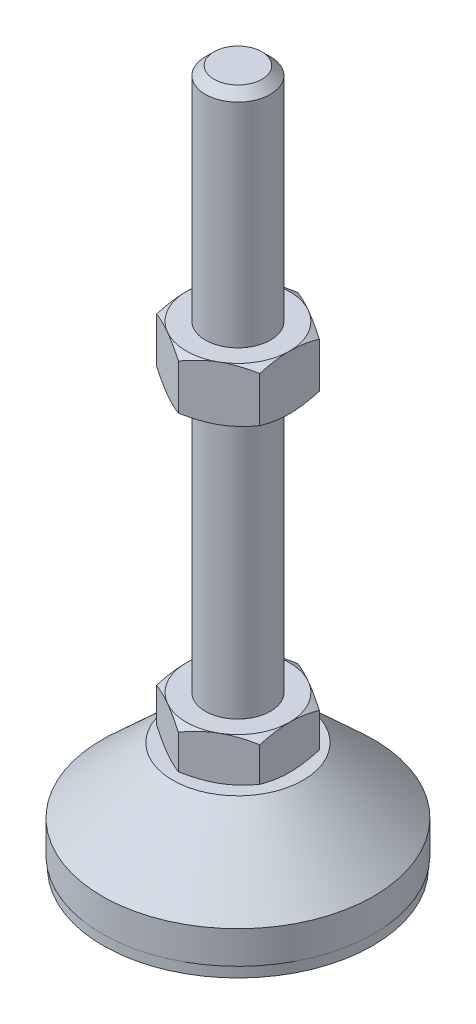
SolidWorks part; units mm, degrees
ref_plane "Спереди" through (0, 0, 0) normal (0, 0, 1) x (1, 0, 0)
ref_plane "Сверху" through (0, 0, 0) normal (0, 1, 0) x (1, 0, 0)
ref_plane "Справа" through (0, 0, 0) normal (1, 0, 0) x (0, 0, -1)
sketch "Эскиз1" plane through (0, 0, 0) normal (0, 0, 1) x (1, 0, 0)
  line L0 (0, 0) -> (-24.8, 0)
  line L1 (-24.8, 0) -> (-24.8, 2)
  line L2 (-24.8, 2) -> (-25, 2)
  line L3 (-25, 2) -> (-25, 8)
  line L4 (-25, 8) -> (-12, 20)
  line L5 (-12, 20) -> (-6, 20)
  line L12 (-6, 28) -> (-6, 126.4)
  line L13 (-6, 126.4) -> (-4.4, 128)
  line L14 (-4.4, 128) -> (0, 128)
  line L15 (0, 128) -> (0, 0) construction
  line L16 (-6, 20) -> (0, 20) construction
  line L17 (0, 0) -> (0, 128)
  line L18 (0, 0) -> (0, -7.9595) construction
  line L19 (-6, 28) -> (-6, 20)
  point P8 (-6, 77.2)
  point P23 (-9, 20)
  dimension "D1" = 12
  dimension "D2" = 20
  dimension "D3" = 8
  dimension "D4" = 50
  dimension "D5" = 6
  dimension "D6" = 1.6
  dimension "D7" = 45
  dimension "D8" = 24
  dimension "D9" = 2
  dimension "D10" = 100
  dimension "D11" = 6
  dimension "D12" = 0.2
revolve "Повернуть1" add sketch "Эскиз1" angle 360 about L17
sketch "Эскиз2" plane through (0, 20, 0) normal (0, 1, 0) x (1, 0, 0)
  line L1 (0, 10.9697) -> (-9.5, 5.4848)
  line L2 (-9.5, 5.4848) -> (-9.5, -5.4848)
  line L3 (-9.5, -5.4848) -> (0, -10.9697)
  line L4 (0, -10.9697) -> (9.5, -5.4848)
  line L5 (9.5, -5.4848) -> (9.5, 5.4848)
  line L6 (9.5, 5.4848) -> (0, 10.9697)
  circle A0 centre (0, 0) radius 9.5 construction
  dimension "D1" = 19
extrude "Бобышка-Вытянуть1" add sketch "Эскиз2" along normal up to vertex (8 mm away) up to point (-6, 28, 0)
ref_plane "Плоскость1" through (0, 77.2, 0) normal (0, 1, 0) x (1, 0, 0)
sketch "Эскиз3" plane through (0, 77.2, 0) normal (0, 1, 0) x (1, 0, 0)
  line L6 (9.5, 5.4848) -> (0, 10.9697)
  line L7 (0, 10.9697) -> (-9.5, 5.4848)
  line L8 (-9.5, 5.4848) -> (-9.5, -5.4848)
  line L9 (-9.5, -5.4848) -> (0, -10.9697)
  line L10 (0, -10.9697) -> (9.5, -5.4848)
  line L11 (9.5, -5.4848) -> (9.5, 5.4848)
  line L12 (9.5, 5.4848) -> (0, 10.9697)
  line L13 (0, 10.9697) -> (-9.5, 5.4848)
  line L14 (-9.5, 5.4848) -> (-9.5, -5.4848)
  line L15 (-9.5, -5.4848) -> (0, -10.9697)
  line L16 (0, -10.9697) -> (9.5, -5.4848)
  line L17 (9.5, -5.4848) -> (9.5, 5.4848)
  dimension "D1" = 0
extrude "Бобышка-Вытянуть2" add sketch "Эскиз3" along normal blind 10
sketch "Эскиз4" plane through (0, 0, 0) normal (0, 0, 1) x (1, 0, 0)
  line L0 (-9.5, 87.2) -> (-18.1603, 82.2)
  line L1 (-18.1603, 82.2) -> (-18.1603, 87.2)
  line L2 (-18.1603, 87.2) -> (-9.5, 87.2)
  line L3 (-18.1603, 82.2) -> (-9.5, 77.2)
  line L4 (50, 77.2) -> (-50, 77.2) construction
  line L5 (-9.5, 77.2) -> (-18.1603, 77.2)
  line L6 (-18.1603, 77.2) -> (-18.1603, 82.2)
  line L7 (-9.5, 87.2) -> (-9.5, 77.2) construction
  line L8 (-9.5, 28) -> (-16.4282, 28)
  line L9 (-16.4282, 28) -> (-16.4282, 24)
  line L10 (-16.4282, 24) -> (-9.5, 28)
  line L11 (-9.5, 20) -> (-16.4282, 24)
  line L12 (-16.4282, 24) -> (-16.4282, 20)
  line L13 (-16.4282, 20) -> (-9.5, 20)
  line L14 (0, 128) -> (0, 96.3793) construction
  dimension "D1" = 30
  dimension "D2" = 30
revolve "Вырез-Повернуть2" cut sketch "Эскиз4" angle 360 about L14
